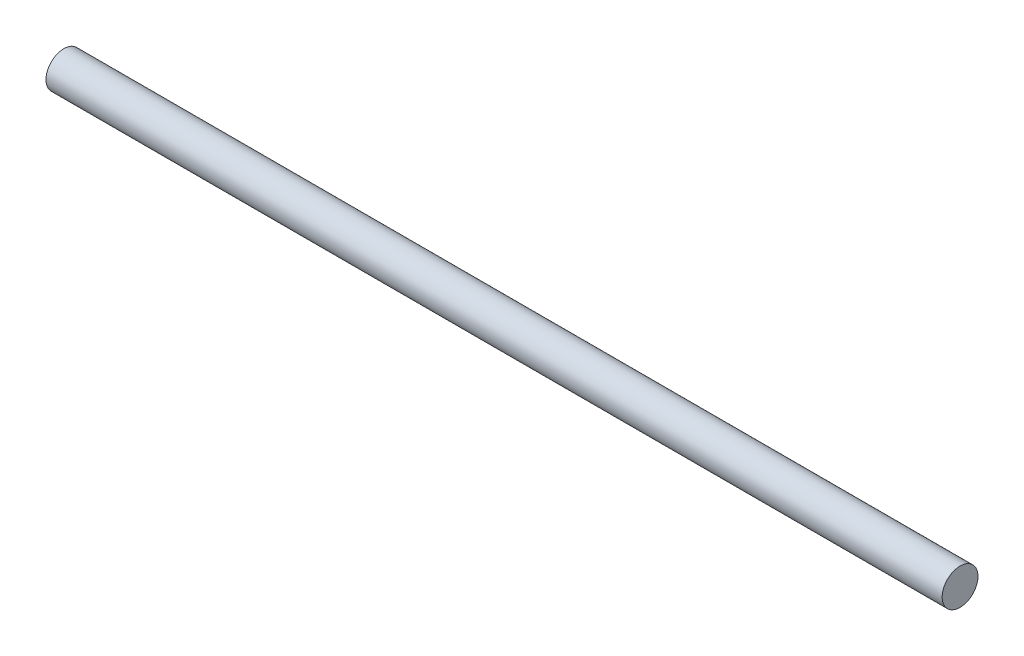
SolidWorks part; units mm, degrees
material "AISI 316 Annealed Stainless Steel Bar (SS)"
ref_plane "Plane1" through (0, 0, 0) normal (0, 0, 1) x (1, 0, 0)
ref_plane "Plane2" through (0, 0, 0) normal (0, 1, 0) x (1, 0, 0)
ref_plane "Plane3" through (0, 0, 0) normal (1, 0, 0) x (0, 0, -1)
sketch "Sketch1" plane through (0, 0, 0) normal (1, 0, 0) x (0, 0, -1)
  circle A0 centre (0, 0) radius 4
  dimension "D1" = 8
extrude "Boss-Extrude1" add sketch "Sketch1" along normal blind 200
